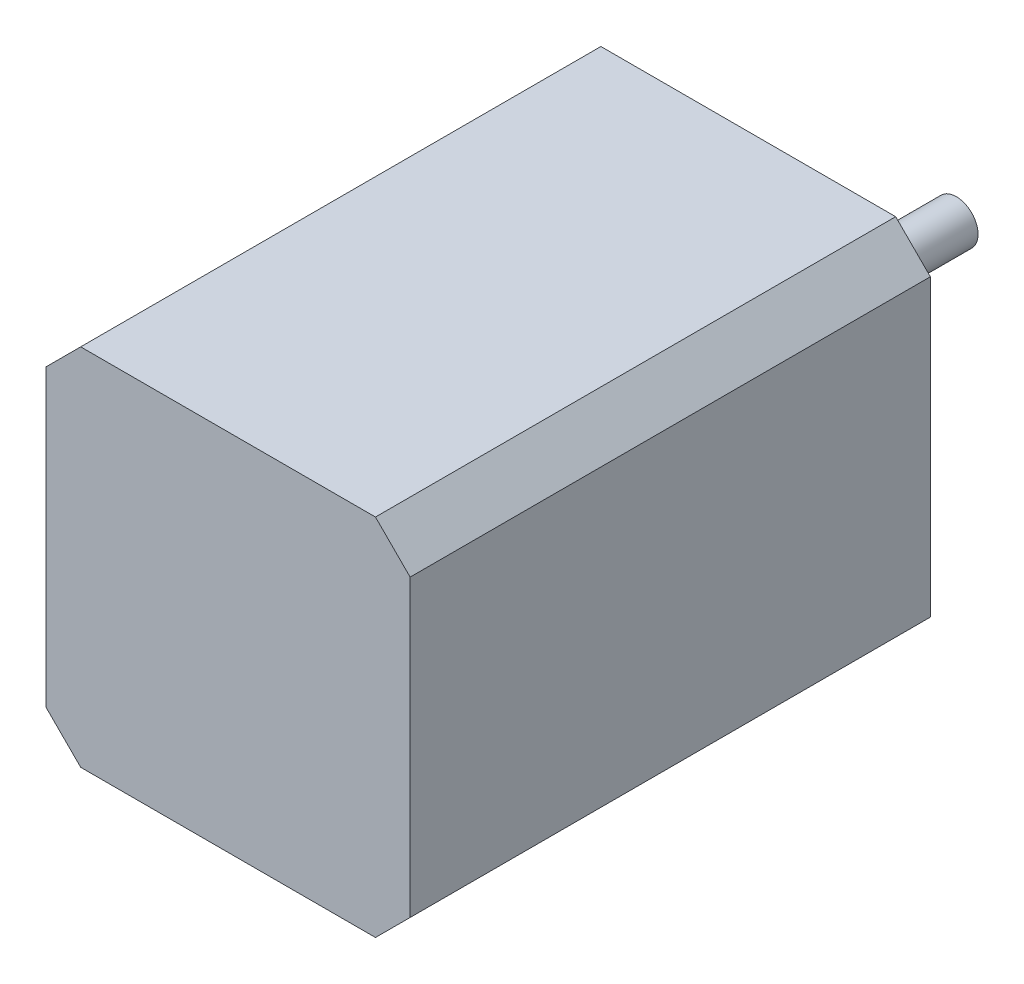
SolidWorks part; units mm, degrees
ref_plane "Спереди" through (0, 0, 0) normal (0, 0, 1) x (1, 0, 0)
ref_plane "Сверху" through (0, 0, 0) normal (0, 1, 0) x (1, 0, 0)
ref_plane "Справа" through (0, 0, 0) normal (1, 0, 0) x (0, 0, -1)
sketch "Эскиз1" plane through (0, 0, 0) normal (0, 0, 1) x (1, 0, 0)
  line L1 (-21, -21) -> (21, -21)
  line L2 (-21, -21) -> (-21, 21)
  line L3 (-21, 21) -> (21, 21)
  line L4 (21, -21) -> (21, 21)
  line L5 (-21, -21) -> (21, 21) construction
  line L6 (-21, 21) -> (21, -21) construction
  point P0 (0, 0)
  dimension "D1" = 42
extrude "Бобышка-Вытянуть1" add sketch "Эскиз1" along normal blind 60
ref_plane "Плоскость1" through (0, 0, 30) normal (0, 0, -1) x (-1, 0, 0)
sketch "Эскиз8" plane through (0, 0, 0) normal (0, 0, -1) x (-1, 0, 0)
  circle A0 centre (0, 0) radius 2.5
  dimension "D1" = 5
extrude "Бобышка-Вытянуть2" add sketch "Эскиз8" along normal blind 24
hole_wizard "Отверстие обработанное метчиком M32" positions "Эскиз11" profile "Эскиз9" tap size "M3" standard "Iso"
sketch "Эскиз11" plane through (0, 0, 0) normal (0, 0, -1) x (-1, 0, 0)
  line L0 (21, 21) -> (21, -21) construction
  line L1 (21, -21) -> (-21, -21) construction
  point P0 (15.5, -15.5)
  dimension "D1" = 5.5
  dimension "D2" = 5.5
sketch "Эскиз9" plane through (-15.5, -15.5, 0) normal (1, 0, 0) x (0, 1, 0)
  line L0 (0, 0) -> (0, 8.2511)
  line L1 (0, 8.2511) -> (1.25, 7.5)
  line L2 (1.25, 7.5) -> (1.25, 0)
  line L5 (1.25, 0) -> (0, 0)
  line L10 (0, 8.2511) -> (-1.25, 7.5) construction
  line L11 (0, -6.35) -> (0, 107.95) construction
  dimension "Диаметр сверла" = 2.5
  dimension "Глубина сверла" = 7.5
  dimension "Угол заточки сверла" = 118
sketch "Эскиз3" plane through (0, 0, 60) normal (0, 0, 1) x (1, 0, 0)
  line L0 (-21, 17) -> (-17, 21)
  line L1 (-21, 21) -> (-21, -21) construction
  line L2 (21, 21) -> (-21, 21) construction
  line L3 (-17, 21) -> (-21, 21)
  line L4 (-21, 21) -> (-21, 17)
  dimension "D1" = 4
extrude "Вырез-Вытянуть1" cut sketch "Эскиз3" against normal through all
pattern_circular "Круговой массив1" count 4 over 360 about axis through (0, 0, 0) along (0, 0, 1) of "Вырез-Вытянуть1", "Отверстие обработанное метчиком M32"
sketch "Эскиз12" plane through (0, 0, 0) normal (0, 0, -1) x (-1, 0, 0)
  circle A0 centre (0, 0) radius 11
  dimension "D1" = 22
extrude "Бобышка-Вытянуть3" add sketch "Эскиз12" along normal blind 2
